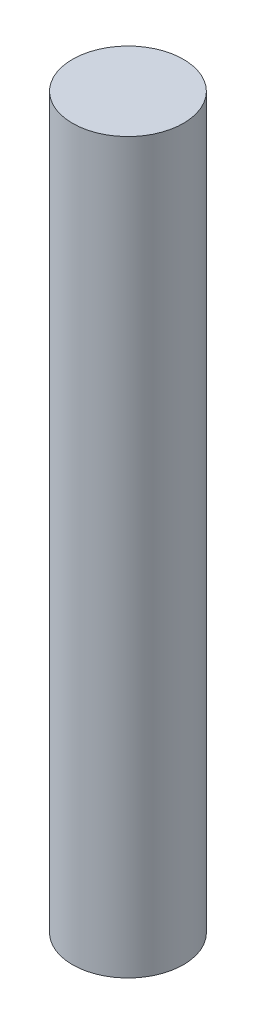
SolidWorks part; units mm, degrees
ref_plane "Front Plane" through (0, 0, 0) normal (0, 0, 1) x (1, 0, 0)
ref_plane "Top Plane" through (0, 0, 0) normal (0, 1, 0) x (1, 0, 0)
ref_plane "Right Plane" through (0, 0, 0) normal (1, 0, 0) x (0, 0, -1)
sketch "Sketch1" plane through (0, 0, 0) normal (0, 1, 0) x (1, 0, 0)
  circle A0 centre (0, 0) radius 40.4114
  dimension "D1" = 80.8228
extrude "Boss-Extrude1" add sketch "Sketch1" along normal blind 530.86
equation "\"Motor_Length\"= 20.90in"
equation "\"Motor_OD\"= 3.182in"
equation "\"D1@Sketch1\"=\"Motor_OD\""
equation "\"D1@Boss-Extrude1\"=\"Motor_Length\""
